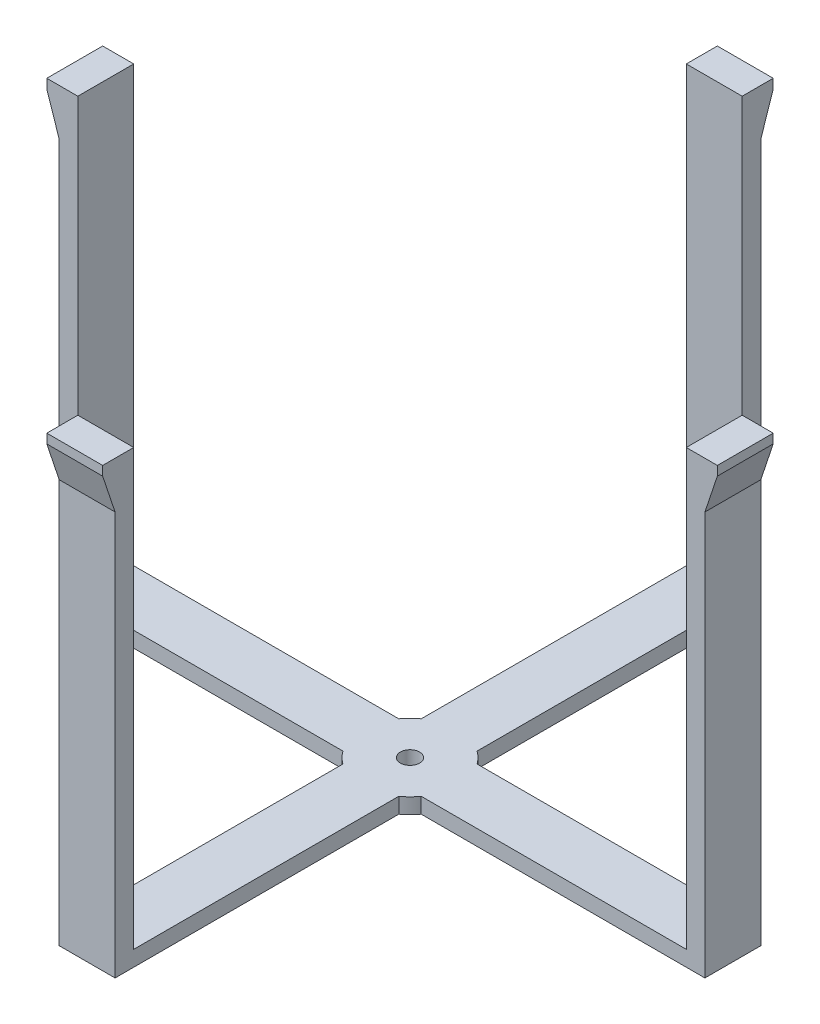
SolidWorks part; units mm, degrees
material "6061-T6 (SS)"
ref_plane "Front Plane" through (0, 0, 0) normal (0, 0, 1) x (1, 0, 0)
ref_plane "Top Plane" through (0, 0, 0) normal (0, 1, 0) x (1, 0, 0)
ref_plane "Right Plane" through (0, 0, 0) normal (1, 0, 0) x (0, 0, -1)
sketch "Sketch5" plane through (0, 0, 0) normal (0, 1, 0) x (1, 0, 0)
  line L0 (-16.0267, 11.43) -> (-132.08, 11.43)
  line L3 (-16.0267, -11.43) -> (-132.08, -11.43)
  line L4 (11.43, 16.0267) -> (11.43, 132.08)
  line L5 (-11.43, 16.0267) -> (-11.43, 132.08)
  line L6 (16.0267, -11.43) -> (132.08, -11.43)
  line L7 (16.0267, 11.43) -> (132.08, 11.43)
  line L8 (-11.43, -16.0267) -> (-11.43, -132.08)
  line L9 (11.43, -16.0267) -> (11.43, -132.08)
  line L10 (-132.08, 11.43) -> (-132.08, -11.43)
  line L11 (11.43, 132.08) -> (-11.43, 132.08)
  line L12 (132.08, -11.43) -> (132.08, 11.43)
  line L13 (-11.43, -132.08) -> (11.43, -132.08)
  arc A4 (-16.0267, -11.43) -> (-11.43, -16.0267) centre (0, 0) ccw
  arc A5 (-11.43, 16.0267) -> (-16.0267, 11.43) centre (0, 0) ccw
  arc A6 (16.0267, 11.43) -> (11.43, 16.0267) centre (0, 0) ccw
  arc A7 (11.43, -16.0267) -> (16.0267, -11.43) centre (0, 0) ccw
  point P1 (132.08, 0)
  point P22 (0, 0)
  point P28 (0, 0)
  dimension "D3" = 19.685
  dimension "D4" = 22.86
  dimension "D5" = 264.16
  dimension "D1" = 4
  dimension "D2" = 4
extrude "Boss-Extrude3" add sketch "Sketch5" along normal blind 6.35
sketch "Sketch7" plane through (0, 6.35, 0) normal (0, 1, 0) x (1, 0, 0)
  circle A0 centre (0, 0) radius 3.937
  dimension "D1" = 7.874
sketch "Sketch8" plane through (0, 6.35, 0) normal (0, 1, 0) x (1, 0, 0)
  line L1 (-11.43, -16.0267) -> (-11.43, -132.08) construction
  line L3 (11.43, -132.08) -> (11.43, -16.0267) construction
  line L4 (11.43, -124.46) -> (-11.43, -124.46)
  line L7 (-11.43, -124.46) -> (-11.43, -132.08)
  line L8 (-11.43, -132.08) -> (11.43, -132.08)
  line L9 (11.43, -132.08) -> (11.43, -124.46)
  dimension "D1" = 7.62
sketch "Sketch9" plane through (0, 6.35, 0) normal (0, 1, 0) x (1, 0, 0)
  circle A0 centre (0, 0) radius 3.937
  dimension "D1" = 7.874
extrude "Cut-Extrude4" cut sketch "Sketch9" against normal blind 127
extrude "Boss-Extrude4" add sketch "Sketch8" along normal blind 177.8
pattern_circular "CirPattern1" count 4 over 360 about axis through (0, 0, 0) along (0, 1, 0) of "Boss-Extrude4"
sketch "Sketch13" plane through (0, 0, 11.43) normal (0, 0, 1) x (1, 0, 0)
  line L18 (-132.08, 184.15) -> (-137.16, 184.15)
  line L19 (-137.16, 184.15) -> (-137.16, 180.34)
  line L20 (-137.16, 180.34) -> (-132.08, 165.1)
  line L21 (-132.08, 184.15) -> (-132.08, 0) construction
  line L22 (-132.08, 165.1) -> (-132.08, 184.15)
  dimension "D1" = 3.81
  dimension "D2" = 5.08
  dimension "D3" = 19.05
extrude "Boss-Extrude6" add sketch "Sketch13" against normal blind 22.86
pattern_circular "CirPattern2" count 4 over 360 about axis through (0, 0, 0) along (0, 1, 0) of "Boss-Extrude6"
equation "\"RocketDiameter\"= 12"
equation "\"Rod_Width\"= .31"
equation "\"D1@Sketch7\"=\"Rod_Width\""
equation "\"D3@Sketch5\"=\"Rod_Width\"*2.5"
equation "\"D1@Sketch9\"=\"Rod_Width\""
equation "\"Rocket Thickness\"= .5"
equation "\"Arm Thickness\"= .25"
equation "\"D1@Sketch8\"=.30"
equation "\"D5@Sketch5\"=10.40"
